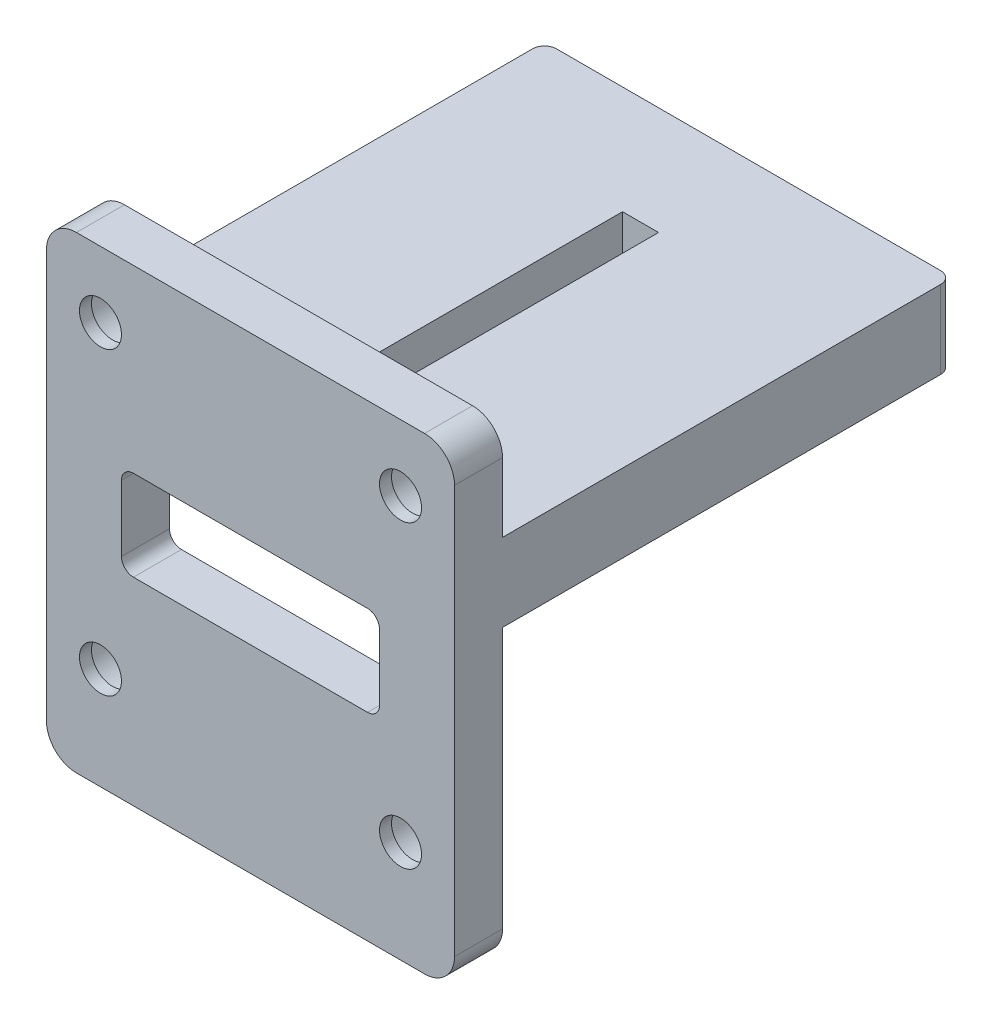
SolidWorks part; units mm, degrees
ref_plane "Front Plane" through (0, 0, 0) normal (0, 0, 1) x (1, 0, 0)
ref_plane "Top Plane" through (0, 0, 0) normal (0, 1, 0) x (1, 0, 0)
ref_plane "Right Plane" through (0, 0, 0) normal (1, 0, 0) x (0, 0, -1)
sketch "Sketch1" plane through (0, 0, 0) normal (0, 0, 1) x (1, 0, 0)
  line L1 (-34, 39) -> (34, 39)
  line L2 (-34, 39) -> (-34, -39)
  line L3 (-34, -39) -> (34, -39)
  line L4 (34, 39) -> (34, -39)
  line L5 (-34, 39) -> (34, -39) construction
  line L6 (-34, -39) -> (34, 39) construction
  point P0 (0, 0)
  dimension "D1" = 68
  dimension "D2" = 78
extrude "Boss-Extrude1" add sketch "Sketch1" along normal blind 8
sketch "Sketch2" plane through (0, 0, 0) normal (0, 0, -1) x (-1, 0, 0)
  line L0 (-34, -39) -> (-34, 39) construction
  line L1 (-34, 22.5) -> (34, 22.5)
  line L2 (-34, 22.5) -> (-34, 9.5)
  line L4 (34, 22.5) -> (34, 9.5)
  line L5 (34, 39) -> (34, -39) construction
  line L6 (-34, 22.5) -> (34, 9.5) construction
  line L7 (0, 16) -> (34, 16) construction
  line L8 (-34, 39) -> (34, 39) construction
  line L9 (-34, 9.5) -> (-19.5, 9.5)
  line L10 (-19.5, 9.5) -> (-19.5, 15.5)
  line L11 (-19.5, 15.5) -> (19.5, 15.5)
  line L12 (19.5, 15.5) -> (19.5, 9.5)
  line L13 (19.5, 9.5) -> (34, 9.5)
  dimension "D1" = 23
  dimension "D2" = 39
  dimension "D3" = 6
  dimension "D4" = 13
extrude "Boss-Extrude2" add sketch "Sketch2" along normal blind 75
sketch "Sketch3" plane through (0, 0, 8) normal (0, 0, 1) x (1, 0, 0)
  line L0 (34, 39) -> (-34, 39) construction
  line L1 (-21.5, 9) -> (21.5, 9)
  line L2 (-21.5, 9) -> (-21.5, -6)
  line L3 (-21.5, -6) -> (21.5, -6)
  line L4 (21.5, 9) -> (21.5, -6)
  line L5 (0, 39) -> (0, 9) construction
  dimension "D1" = 15
  dimension "D2" = 30
  dimension "D3" = 43
extrude "Cut-Extrude1" cut sketch "Sketch3" against normal up to next
fillet "Fillet1" radius 2 6 edges at (-21.5, -6, 4) (21.5, -6, 4) (21.5, 9, 4) (-21.5, 9, 4) (-34, 16, -75) (34, 16, -75)
fillet "Fillet2" radius 5 4 edges at (34, 39, 4) (34, -39, 4) (-34, -39, 4) (-34, 39, 4)
sketch "Sketch4" plane through (0, 22.5, 0) normal (0, 1, 0) x (1, 0, 0)
  line L0 (-32, 75) -> (32, 75) construction
  line L1 (-3, 57) -> (3, 57)
  line L2 (-3, 57) -> (-3, 12)
  line L3 (-3, 12) -> (3, 12)
  line L4 (3, 57) -> (3, 12)
  line L5 (0, 57) -> (0, 75) construction
  dimension "D1" = 6
  dimension "D2" = 45
  dimension "D3" = 18
extrude "Cut-Extrude2" cut sketch "Sketch4" against normal through all
sketch "Sketch5" plane through (0, 0, 0) normal (0, 0, -1) x (-1, 0, 0)
  line L0 (0, 39) -> (0, 28) construction
  line L1 (-25, 28) -> (25, 28) construction
  line L2 (-25, 28) -> (-25, -22) construction
  line L3 (-25, -22) -> (25, -22) construction
  line L4 (25, 28) -> (25, -22) construction
  line L5 (-29, 39) -> (29, 39) construction
  circle A0 centre (-25, 28) radius 3.5
  circle A1 centre (25, 28) radius 3.5
  circle A2 centre (-25, -22) radius 3.5
  circle A3 centre (25, -22) radius 3.5
  dimension "D3" = 7
  dimension "D1" = 50
  dimension "D2" = 11
extrude "Cut-Extrude3" cut sketch "Sketch5" against normal through all
sketch "Sketch7" plane through (0, 0, 0) normal (0, 0, -1) x (-1, 0, 0)
  circle A0 centre (-25, 28) radius 5.5
  circle A1 centre (25, 28) radius 5.5
  circle A2 centre (-25, -22) radius 5.5
  circle A3 centre (25, -22) radius 5.5
  dimension "D1" = 11
extrude "Cut-Extrude4" cut sketch "Sketch7" against normal blind 6
